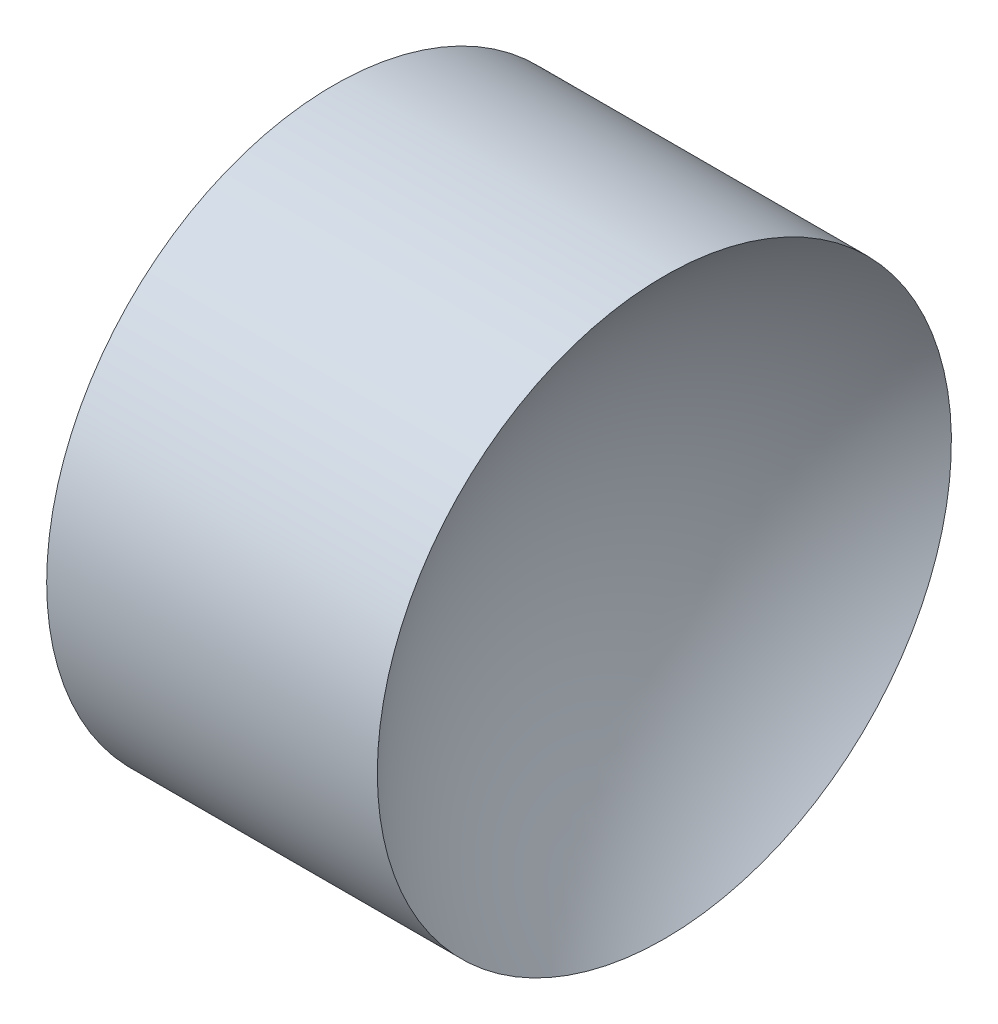
SolidWorks part; units mm, degrees
ref_plane "前视基准面" through (0, 0, 0) normal (0, 0, 1) x (1, 0, 0)
ref_plane "上视基准面" through (0, 0, 0) normal (0, 1, 0) x (1, 0, 0)
ref_plane "右视基准面" through (0, 0, 0) normal (1, 0, 0) x (0, 0, -1)
sketch "草图1" plane through (0, 0, 0) normal (0, 0, 1) x (1, 0, 0)
  line L0 (10.5782, 6.5156) -> (13.4181, 6.5156) construction
  line L1 (11.0806, 6.5156) -> (11.0806, 8.5156)
  line L2 (11.0806, 8.5156) -> (13.3844, 8.5156)
  line L3 (12.5806, 6.5156) -> (11.0806, 6.5156)
  arc A0 (13.3844, 8.5156) -> (12.5806, 6.5156) centre (15.4706, 6.5156) ccw
  dimension "D3" = 2.89
  dimension "D1" = 2
  dimension "D2" = 2.3038
revolve "旋转1" add sketch "草图1" angle 360 about L0
